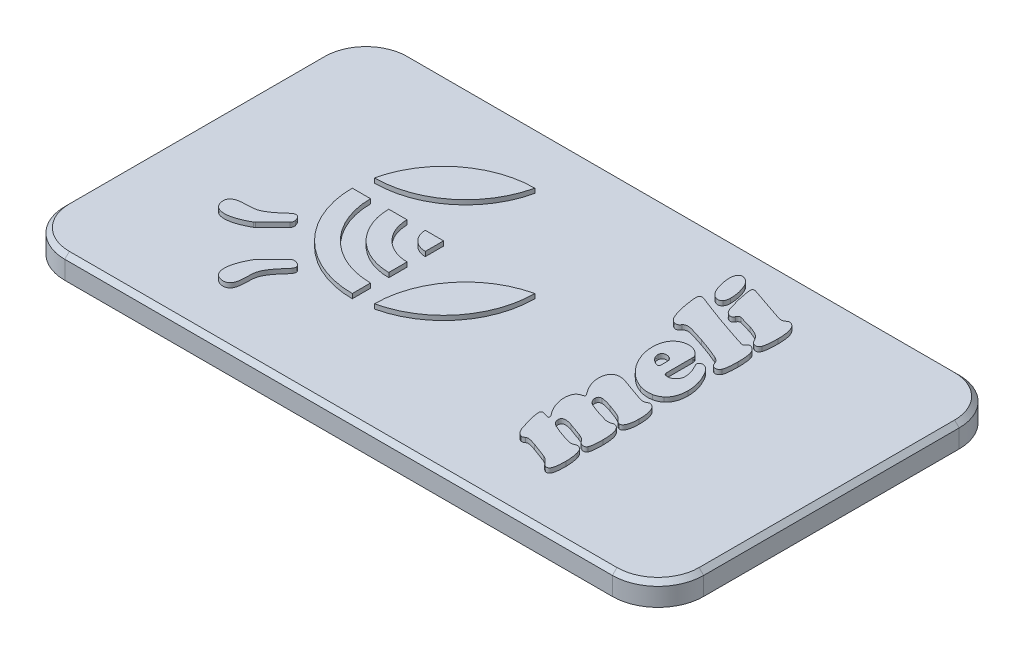
SolidWorks part; units mm, degrees
ref_plane "Front" through (0, 0, 0) normal (0, 0, 1) x (1, 0, 0)
ref_plane "Top" through (0, 0, 0) normal (0, 1, 0) x (1, 0, 0)
ref_plane "Right" through (0, 0, 0) normal (1, 0, 0) x (0, 0, -1)
sketch "Sketch1" plane through (0, 0, 0) normal (0, 1, 0) x (1, 0, 0)
  line L1 (0, 0) -> (140, 0)
  line L2 (0, 0) -> (0, 76)
  line L3 (0, 76) -> (140, 76)
  line L4 (140, 0) -> (140, 76)
  dimension "D1" = 140
  dimension "D2" = 76
extrude "Boss-Extrude1" add sketch "Sketch1" along normal blind 5
fillet "Fillet1" radius 10 4 edges at (0, 2.5, -76) (140, 2.5, -76) (140, 2.5, 0) (0, 2.5, 0)
sketch "Sketch3" plane through (0, 0, 0) normal (0, -1, 0) x (1, 0, 0)
  line L8 (5.2, -10) -> (5.2, -66)
  line L9 (10, -70.8) -> (130, -70.8)
  line L10 (134.8, -66) -> (134.8, -10)
  line L11 (130, -5.2) -> (10, -5.2)
  line L12 (5.2, -10) -> (5.2, -66)
  line L13 (10, -70.8) -> (130, -70.8)
  line L14 (134.8, -66) -> (134.8, -10)
  line L15 (130, -5.2) -> (10, -5.2)
  arc A8 (5.2, -66) -> (10, -70.8) centre (10, -66) ccw
  arc A9 (130, -70.8) -> (134.8, -66) centre (130, -66) ccw
  arc A10 (134.8, -10) -> (130, -5.2) centre (130, -10) ccw
  arc A11 (10, -5.2) -> (5.2, -10) centre (10, -10) ccw
  arc A12 (5.2, -66) -> (10, -70.8) centre (10, -66) ccw
  arc A13 (130, -70.8) -> (134.8, -66) centre (130, -66) ccw
  arc A14 (134.8, -10) -> (130, -5.2) centre (130, -10) ccw
  arc A15 (10, -5.2) -> (5.2, -10) centre (10, -10) ccw
  dimension "D1" = 5.2
extrude "Boss-Extrude2" add sketch "Sketch3" along normal blind 4
sketch "Sketch4" plane through (0, 5, 0) normal (0, 1, 0) x (1, 0, 0)
  line L0 (105, 69.969) -> (105, 6.031) construction
  line L1 (0, 38) -> (140, 38) construction
  line L2 (0, 66) -> (0, 10) construction
  line L3 (140, 10) -> (140, 66) construction
  text T0 "meli" font "Cooper Black" height in points 72
  dimension "D1" = 35
extrude "Boss-Extrude3" add sketch "Sketch4" along normal blind 1
sketch "Sketch5" plane through (0, 5, 0) normal (0, 1, 0) x (1, 0, 0)
  line L0 (50, 43) -> (50, 39)
  line L1 (50, 43) -> (46, 43)
  line L2 (50, 35) -> (50, 31)
  line L3 (42, 43) -> (38, 43)
  line L4 (34, 43) -> (30, 43)
  line L5 (50, 27) -> (50, 23)
  line L6 (50, 63) -> (30.4844, 47.375) construction
  line L7 (50, 43) -> (63.8543, 56.8543) construction
  line L8 (50, 43) -> (35.8579, 28.8579) construction
  line L9 (29.6212, 29.6923) -> (25.848, 25.919)
  line L10 (36.6923, 22.6212) -> (32.919, 18.848)
  arc A0 (50, 63) -> (30.4844, 47.375) centre (50, 43) ccw
  arc A1 (34, 43) -> (50, 27) centre (50, 43) ccw
  arc A2 (38, 43) -> (50, 31) centre (50, 43) ccw
  arc A3 (42, 43) -> (50, 35) centre (50, 43) ccw
  arc A4 (46, 43) -> (50, 39) centre (50, 43) ccw
  arc A5 (50, 63) -> (30.4844, 47.375) centre (30.4844, 67.375) cw
  arc A6 (30, 43) -> (50, 23) centre (50, 43) ccw
  arc A7 (70, 43) -> (54.375, 23.4844) centre (74.375, 23.4844) ccw
  arc A8 (70, 43) -> (54.375, 23.4844) centre (50, 43) cw
  arc A9 (37.6401, 22.8847) -> (36.6923, 22.6212) centre (37.3994, 21.9141) ccw
  arc A10 (32.7615, 18.6432) -> (32.919, 18.848) centre (33.6261, 18.1409) cw
  arc A11 (29.6212, 29.6923) -> (29.8847, 30.6401) centre (28.9141, 30.3994) ccw
  arc A12 (25.848, 25.919) -> (25.6432, 25.7615) centre (25.1409, 26.6261) cw
  spline S0 degree 3 poles (32.7615, 18.6432) (31.021, 15.6476) (30.1969, 11.5645) (34.3114, 11.0827) (35.0652, 12.2211) (35.3516, 14.6689) (35.0571, 16.9433) (37.1422, 19.6028) (39.1703, 21.7386) (38.6479, 22.6348) (37.6401, 22.8847) knots 0.004098 0.004098 0.004098 0.004098 0.326132 0.390384 0.476516 0.501151 0.636741 0.847835 0.912464 0.98744 0.98744 0.98744 0.98744
  spline S1 degree 3 poles (25.6432, 25.7615) (22.6476, 24.021) (18.5645, 23.1969) (18.0827, 27.3114) (19.2211, 28.0652) (21.6689, 28.3516) (23.9433, 28.0571) (26.6028, 30.1422) (28.7386, 32.1703) (29.6348, 31.6479) (29.8847, 30.6401) knots 0.004098 0.004098 0.004098 0.004098 0.326132 0.390384 0.476516 0.501151 0.636741 0.847835 0.912464 0.98744 0.98744 0.98744 0.98744
  dimension "D1" = 40
  dimension "D2" = 25
  dimension "D4" = 1
  dimension "D3" = 5
extrude "Boss-Extrude4" add sketch "Sketch5" along normal blind 1
chamfer "Chamfer1" distance 1 angle 60 8 edges at (70, -4, -70.8) (133.3941, -4, -69.3941) (6.6059, -4, -69.3941) (134.8, -4, -38) (5.2, -4, -38) (133.3941, -4, -6.6059) (6.6059, -4, -6.6059) (70, -4, -5.2)
chamfer "Chamfer2" distance 1 angle 45 8 edges at (137.0711, 5, -73.0711) (70, 5, -76) (140, 5, -38) (2.9289, 5, -73.0711) (137.0711, 5, -2.9289) (0, 5, -38) (70, 5, 0) (2.9289, 5, -2.9289)
